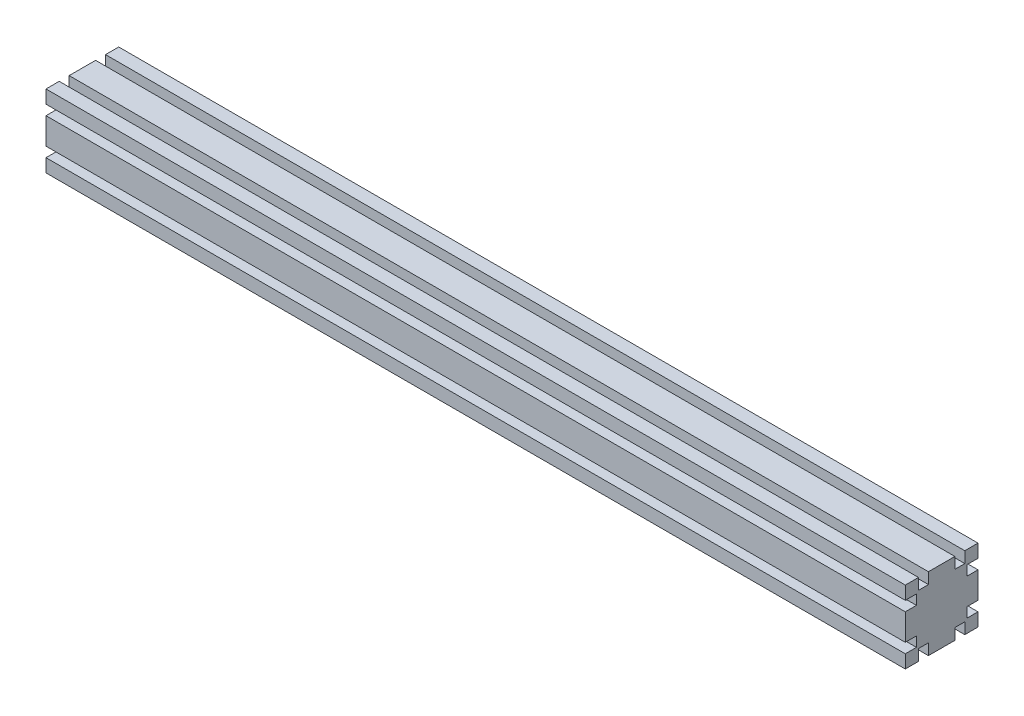
SolidWorks part; units mm, degrees
ref_plane "前视基准面" through (0, 0, 0) normal (0, 0, 1) x (1, 0, 0)
ref_plane "上视基准面" through (0, 0, 0) normal (0, 1, 0) x (1, 0, 0)
ref_plane "右视基准面" through (0, 0, 0) normal (1, 0, 0) x (0, 0, -1)
sketch "草图1" plane through (0, 0, 0) normal (1, 0, 0) x (0, 0, -1)
  line L1 (-30, 30) -> (30, 30)
  line L2 (-30, 30) -> (-30, -30)
  line L3 (-30, -30) -> (30, -30)
  line L4 (30, 30) -> (30, -30)
  line L5 (-30, 30) -> (30, -30) construction
  line L6 (-30, -30) -> (30, 30) construction
  point P0 (0, 0)
  dimension "D1" = 60
  dimension "60" = 60
extrude "凸台-拉伸1" add sketch "草图1" along normal blind 709
sketch "草图2" plane through (0, 0, 0) normal (-1, 0, 0) x (0, 0, 1)
  line L0 (-19.1, 30) -> (-19.1, 20.8)
  line L1 (-30, 30) -> (30, 30) construction
  line L2 (-19.1, 20.8) -> (-10.9, 20.8)
  line L3 (-10.9, 20.8) -> (-10.9, 30)
  line L4 (-19.1, 30) -> (-10.9, 30)
  line L5 (0, -47.1527) -> (0, 0) construction
  line L6 (0, 0) -> (0, 44.4053) construction
  line L7 (0, 0) -> (71.4438, 0) construction
  line L8 (0, 0) -> (-65.6472, 0) construction
  line L9 (-19.1, -20.8) -> (-10.9, -20.8)
  line L10 (-10.9, -20.8) -> (-10.9, -30)
  line L11 (-19.1, -30) -> (-19.1, -20.8)
  line L12 (-19.1, -30) -> (-10.9, -30)
  line L13 (19.1, -30) -> (10.9, -30)
  line L14 (10.9, -20.8) -> (10.9, -30)
  line L15 (19.1, -30) -> (19.1, -20.8)
  line L16 (19.1, -20.8) -> (10.9, -20.8)
  line L17 (19.1, 20.8) -> (10.9, 20.8)
  line L18 (19.1, 30) -> (19.1, 20.8)
  line L19 (19.1, 30) -> (10.9, 30)
  line L20 (10.9, 20.8) -> (10.9, 30)
  line L21 (-30, 19.1) -> (-20.8, 19.1)
  line L22 (-30, -30) -> (-30, 30) construction
  line L23 (-20.8, 19.1) -> (-20.8, 10.9)
  line L24 (-20.8, 10.9) -> (-30, 10.9)
  line L25 (-30, 10.9) -> (-30, 19.1)
  line L26 (-30, -10.9) -> (-30, -19.1)
  line L27 (-20.8, -10.9) -> (-30, -10.9)
  line L28 (-20.8, -19.1) -> (-20.8, -10.9)
  line L29 (-30, -19.1) -> (-20.8, -19.1)
  line L30 (30, -19.1) -> (20.8, -19.1)
  line L31 (20.8, -19.1) -> (20.8, -10.9)
  line L32 (20.8, -10.9) -> (30, -10.9)
  line L33 (30, -10.9) -> (30, -19.1)
  line L34 (30, 10.9) -> (30, 19.1)
  line L35 (20.8, 10.9) -> (30, 10.9)
  line L36 (20.8, 19.1) -> (20.8, 10.9)
  line L37 (30, 19.1) -> (20.8, 19.1)
  dimension "D1" = 10.9
  dimension "D2" = 8.2
  dimension "D3" = 9.2
  dimension "D4" = 8.2
  dimension "D5" = 9.2
  dimension "D6" = 10.9
extrude "切除-拉伸1" cut sketch "草图2" against normal through all
sketch "草图3" plane through (0, -30, 0) normal (0, -1, 0) x (1, 0, 0)
  line L0 (0, 30) -> (60, -30)
  line L1 (709, -30) -> (0, -30) construction
  line L2 (60, -30) -> (0, -30)
  line L3 (0, -30) -> (0, 30)
  line L4 (709, 30) -> (649, -30)
  line L5 (649, -30) -> (709, -30)
  line L6 (709, -30) -> (709, 30)
